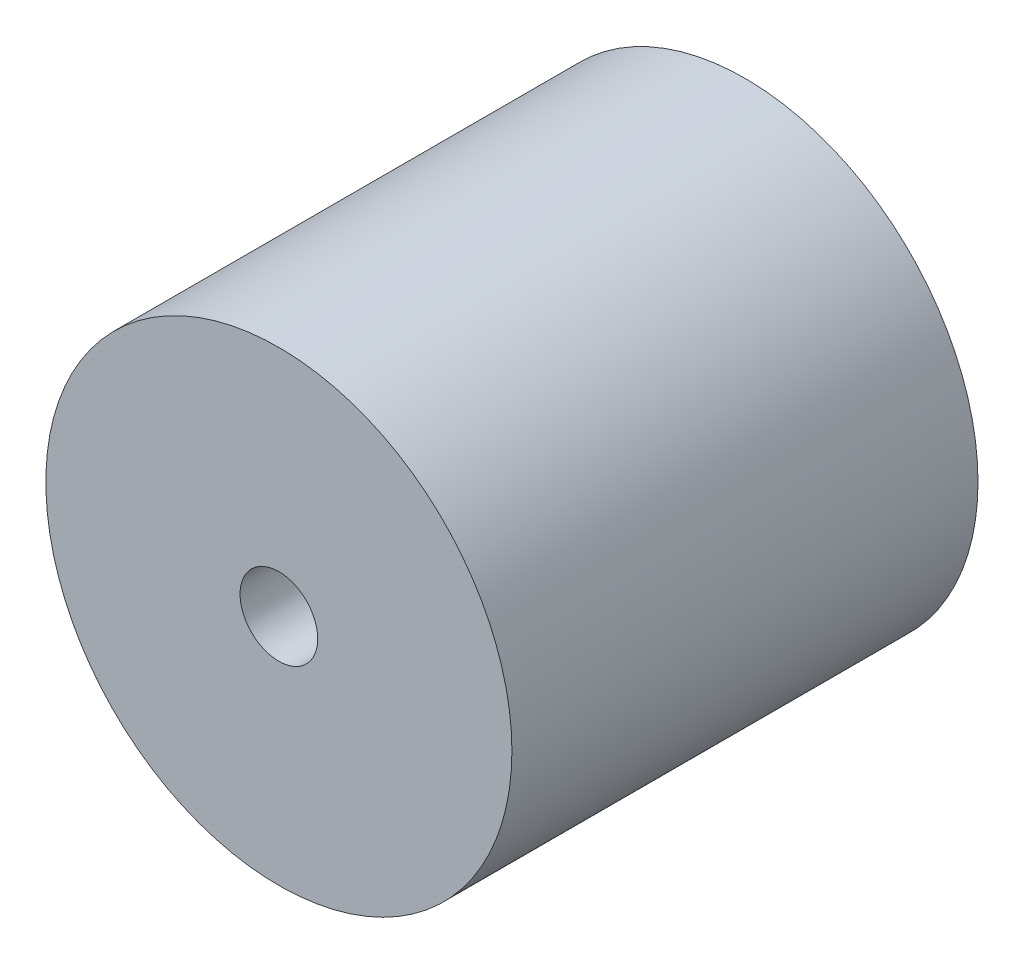
SolidWorks part; units mm, degrees
ref_plane "Plan de face" through (0, 0, 0) normal (0, 0, 1) x (1, 0, 0)
ref_plane "Plan de dessus" through (0, 0, 0) normal (0, 1, 0) x (1, 0, 0)
ref_plane "Plan de droite" through (0, 0, 0) normal (1, 0, 0) x (0, 0, -1)
sketch "Esquisse1" plane through (0, 0, 0) normal (0, 0, 1) x (1, 0, 0)
  circle A0 centre (0, 0) radius 30
  dimension "D1" = 60
extrude "Boss.-Extru.1" add sketch "Esquisse1" along normal blind 60
sketch "Esquisse2" plane through (0, 0, 60) normal (0, 0, 1) x (1, 0, 0)
  circle A0 centre (0, 0) radius 5
  dimension "D1" = 10
extrude "Enlèv. mat.-Extru.1" cut sketch "Esquisse2" against normal blind 60
